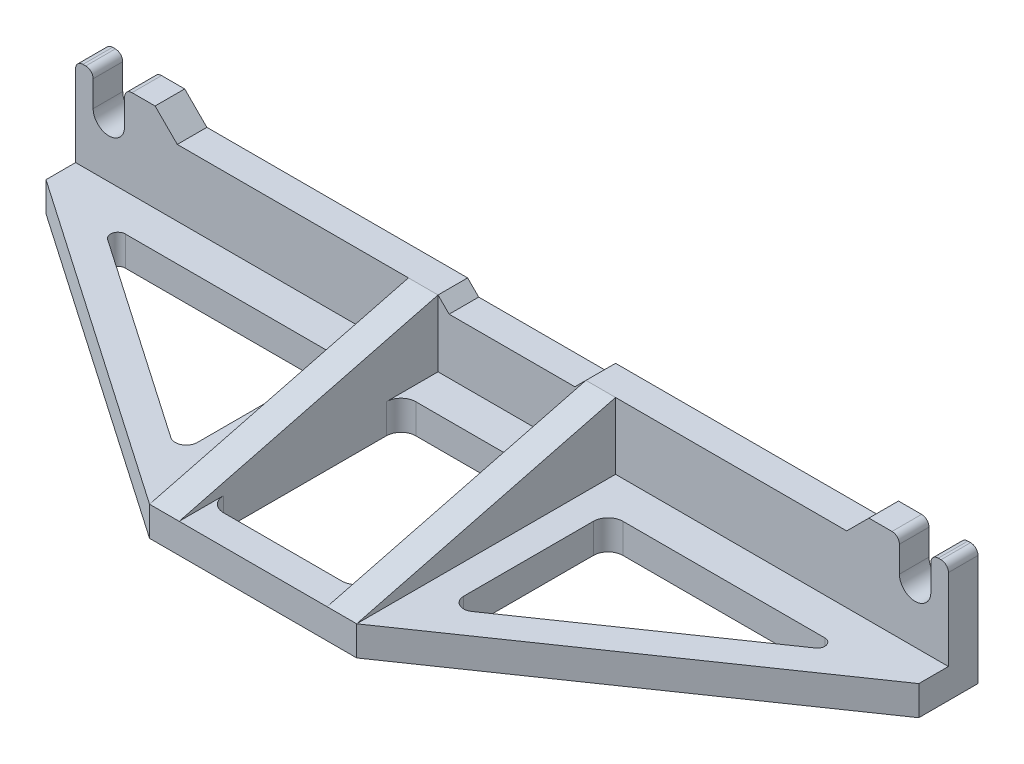
SolidWorks part; units mm, degrees
ref_plane "Front Plane" through (0, 0, 0) normal (0, 0, 1) x (1, 0, 0)
ref_plane "Top Plane" through (0, 0, 0) normal (0, 1, 0) x (1, 0, 0)
ref_plane "Right Plane" through (0, 0, 0) normal (1, 0, 0) x (0, 0, -1)
sketch "Sketch1" plane through (0, 0, 0) normal (0, 0, 1) x (1, 0, 0)
  line L0 (4.25, 0) -> (4.25, 9)
  line L1 (4.25, 9) -> (9, 9)
  line L2 (9, 9) -> (9, -23)
  line L3 (9, -23) -> (-227, -23)
  line L4 (-227, -23) -> (-227, 9)
  line L5 (-213.75, 9) -> (-4.25, 9)
  line L6 (-4.25, 9) -> (-4.25, 0)
  line L7 (-4.25, 9) -> (4.25, 9) construction
  line L8 (-227, 9) -> (-222.25, 9)
  line L9 (-222.25, 9) -> (-222.25, 0)
  line L10 (-213.75, 0) -> (-213.75, 9)
  line L11 (-4.25, 0) -> (4.25, 0) construction
  line L12 (-222.25, 0) -> (-213.75, 0) construction
  line L13 (-213.75, 0) -> (-4.25, 0) construction
  line L14 (-205.5, 9) -> (-199.5, 3)
  line L15 (-199.5, 3) -> (-18.5, 3)
  line L16 (-18.5, 3) -> (-12.5, 9)
  line L17 (-109, 9) -> (-109, 43.7143) construction
  line L18 (-135, 9) -> (-126, 0)
  line L19 (-126, 0) -> (-92, 0)
  line L20 (-92, 0) -> (-83, 9)
  line L21 (-109, 0) -> (-109, 9) construction
  circle A0 centre (0, 0) radius 4.25
  circle A1 centre (-218, 0) radius 4.25
  point P28 (-109, 0)
  dimension "D1" = 8.5
  dimension "D4" = 218
  dimension "D2" = 8.25
  dimension "D3" = 18.75
  dimension "D5" = 236
  dimension "D6" = 8.25
  dimension "D7" = 32
  dimension "D8" = 135
  dimension "D9" = 135
  dimension "D10" = 26
  dimension "D11" = 26
extrude "Boss-Extrude1" add sketch "Sketch1" along normal blind 8 contours A1 L9 L8 L4 L3 L2 L1 L0 A0 L6 L5 L16 L15 L20 L19 L18 L14 L10
sketch "Sketch2" plane through (0, -23, 0) normal (0, -1, 0) x (1, 0, 0)
  line L0 (-227, 8) -> (-227, 16)
  line L1 (-227, 16) -> (-137, 78)
  line L2 (-137, 78) -> (-81, 78)
  line L3 (-81, 78) -> (9, 16)
  line L4 (9, 16) -> (9, 8)
  line L5 (9, 8) -> (-227, 8) construction
  line L6 (9, 8) -> (-227, 8)
  line L7 (-109, 8) -> (-109, 78) construction
  dimension "D1" = 8
  dimension "D2" = 56
  dimension "D3" = 70
extrude "Boss-Extrude2" add sketch "Sketch2" against normal blind 8
ref_plane "Plane1" through (-81, 0, 0) normal (1, 0, 0) x (0, 0, -1)
ref_plane "Plane2" through (-137, 0, 0) normal (1, 0, 0) x (0, 0, -1)
sketch "Sketch4" plane through (-81, 0, 0) normal (1, 0, 0) x (0, 0, -1)
  line L0 (-78, -15) -> (-8, 3)
  line L2 (-8, 0) -> (-8, -15)
  line L3 (-8, -15) -> (-78, -15)
  line L4 (-8, 0) -> (-8, 3) construction
  line L5 (-8, 0) -> (-8, 3)
extrude "Boss-Extrude3" add sketch "Sketch4" against normal blind 8
sketch "Sketch5" plane through (-137, 0, 0) normal (1, 0, 0) x (0, 0, -1)
  line L4 (-8, 3) -> (-78, -15)
  line L5 (-8, 0) -> (-8, 3)
  line L6 (-8, -15) -> (-8, 0)
  line L7 (-78, -15) -> (-8, -15)
  line L8 (-8, 3) -> (-78, -15)
  line L9 (-8, 0) -> (-8, 3)
  line L10 (-8, -15) -> (-8, 0)
  line L11 (-78, -15) -> (-8, -15)
  dimension "D1" = 0
extrude "Boss-Extrude4" add sketch "Sketch5" along normal blind 8
sketch "Sketch6" plane through (0, -15, 0) normal (0, 1, 0) x (1, 0, 0)
  line L0 (-129, -18) -> (-89, -18)
  line L1 (-129, -78) -> (-129, -8) construction
  line L2 (-89, -78) -> (-89, -8) construction
  line L3 (-89, -18) -> (-89, -70)
  line L4 (-89, -8) -> (-89, -78) construction
  line L5 (-89, -70) -> (-129, -70)
  line L6 (-129, -8) -> (-129, -78) construction
  line L7 (-129, -70) -> (-129, -18)
  line L8 (-89, -78) -> (-129, -78) construction
  line L9 (-129, -8) -> (-89, -8) construction
  dimension "D1" = 8
  dimension "D2" = 10
extrude "Cut-Extrude1" cut sketch "Sketch6" against normal through all
sketch "Sketch7" plane through (0, -15, 0) normal (0, 1, 0) x (1, 0, 0)
  line L0 (-73, -18) -> (-8.005, -18)
  line L1 (-8.005, -18) -> (-73, -62.7743)
  line L2 (-73, -62.7743) -> (-73, -18)
  line L3 (-145, -18) -> (-209.995, -18)
  line L4 (-209.995, -18) -> (-145, -62.7743)
  line L5 (-145, -62.7743) -> (-145, -18)
  line L6 (-137, -78) -> (-227, -16) construction
  line L7 (9, -16) -> (-81, -78) construction
  line L8 (-145, -18) -> (-129, -18) construction
  line L9 (-89, -18) -> (-73, -18) construction
  line L10 (-137, -78) -> (-137, -8) construction
  line L11 (-81, -78) -> (-81, -8) construction
  dimension "D1" = 8
  dimension "D2" = 8
  dimension "D3" = 8
  dimension "D4" = 8
extrude "Cut-Extrude2" cut sketch "Sketch7" against normal through all
fillet "Fillet1" radius 4 4 edges at (-73, -19, 18) (-129, -19, 18) (-89, -19, 18) (-145, -19, 18)
fillet "Fillet2" radius 2 2 edges at (-209.995, -19, 18) (-8.005, -19, 18)
fillet "Fillet3" radius 4 2 edges at (-129, -19, 70) (-89, -19, 70)
fillet "Fillet4" radius 3 2 edges at (-73, -19, 62.7743) (-145, -19, 62.7743)
fillet "Fillet5" radius 2 6 edges at (9, 9, 4) (4.25, 9, 4) (-4.25, 9, 4) (-213.75, 9, 4) (-222.25, 9, 4) (-227, 9, 4)
